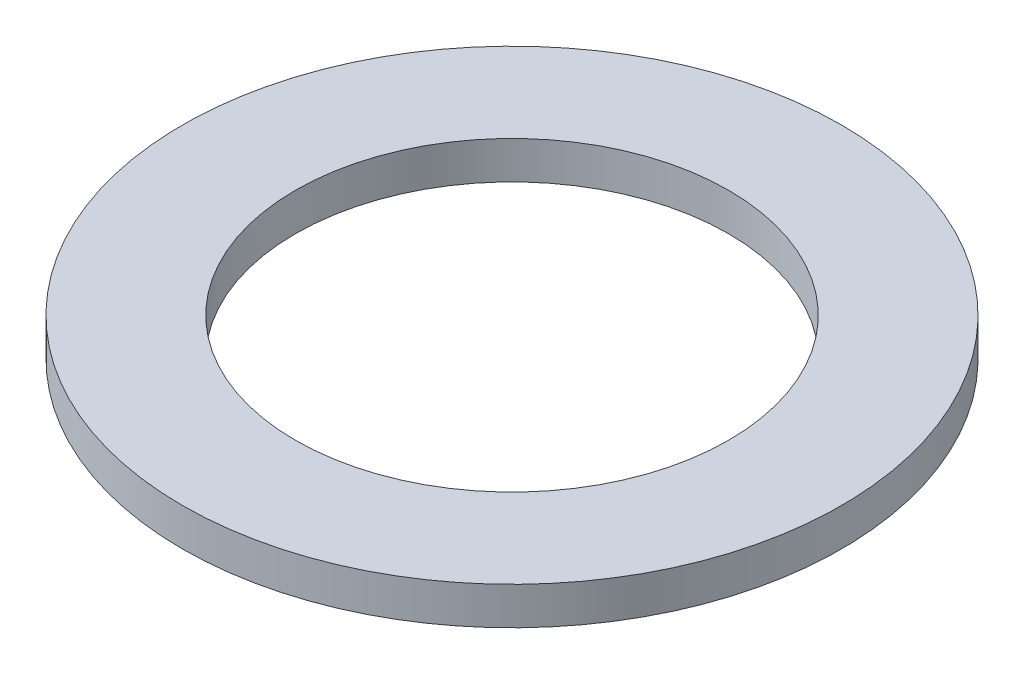
SolidWorks part; units mm, degrees
ref_plane "Front Plane" through (0, 0, 0) normal (0, 0, 1) x (1, 0, 0)
ref_plane "Top Plane" through (0, 0, 0) normal (0, 1, 0) x (1, 0, 0)
ref_plane "Right Plane" through (0, 0, 0) normal (1, 0, 0) x (0, 0, -1)
sketch "Sketch1" plane through (0, 0, 0) normal (0, 1, 0) x (1, 0, 0)
  circle A0 centre (0, 0) radius 1.75
  circle A1 centre (0, 0) radius 1.15
  dimension "D1" = 2.3
  dimension "D2" = 3.5
extrude "Boss-Extrude1" add sketch "Sketch1" along normal blind 0.2
